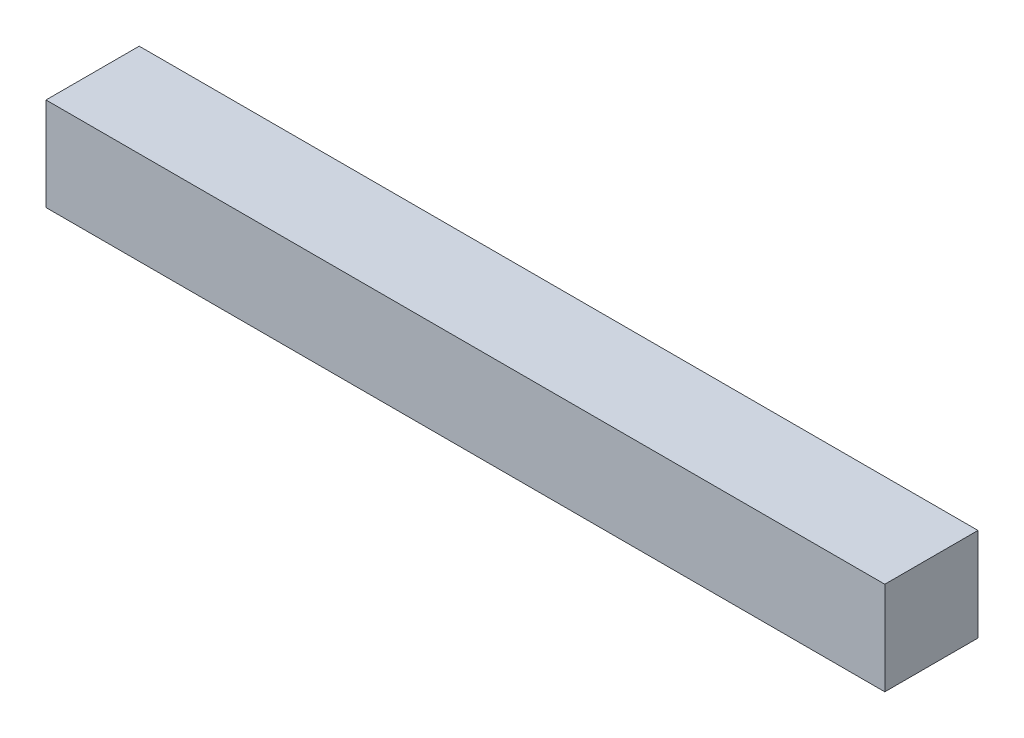
SolidWorks part; units mm, degrees
ref_plane "Front Plane" through (0, 0, 0) normal (0, 0, 1) x (1, 0, 0)
ref_plane "Top Plane" through (0, 0, 0) normal (0, 1, 0) x (1, 0, 0)
ref_plane "Right Plane" through (0, 0, 0) normal (1, 0, 0) x (0, 0, -1)
sketch "Sketch1" plane through (0, 0, 0) normal (0, 1, 0) x (1, 0, 0)
  line L1 (-114.3, -12.7) -> (114.3, -12.7)
  line L2 (-114.3, -12.7) -> (-114.3, 12.7)
  line L3 (-114.3, 12.7) -> (114.3, 12.7)
  line L4 (114.3, -12.7) -> (114.3, 12.7)
  line L5 (-114.3, -12.7) -> (114.3, 12.7) construction
  line L6 (-114.3, 12.7) -> (114.3, -12.7) construction
  point P0 (0, 0)
  dimension "D1" = 25.4
  dimension "D2" = 228.6
extrude "Boss-Extrude2" add sketch "Sketch1" along normal blind 25.4
